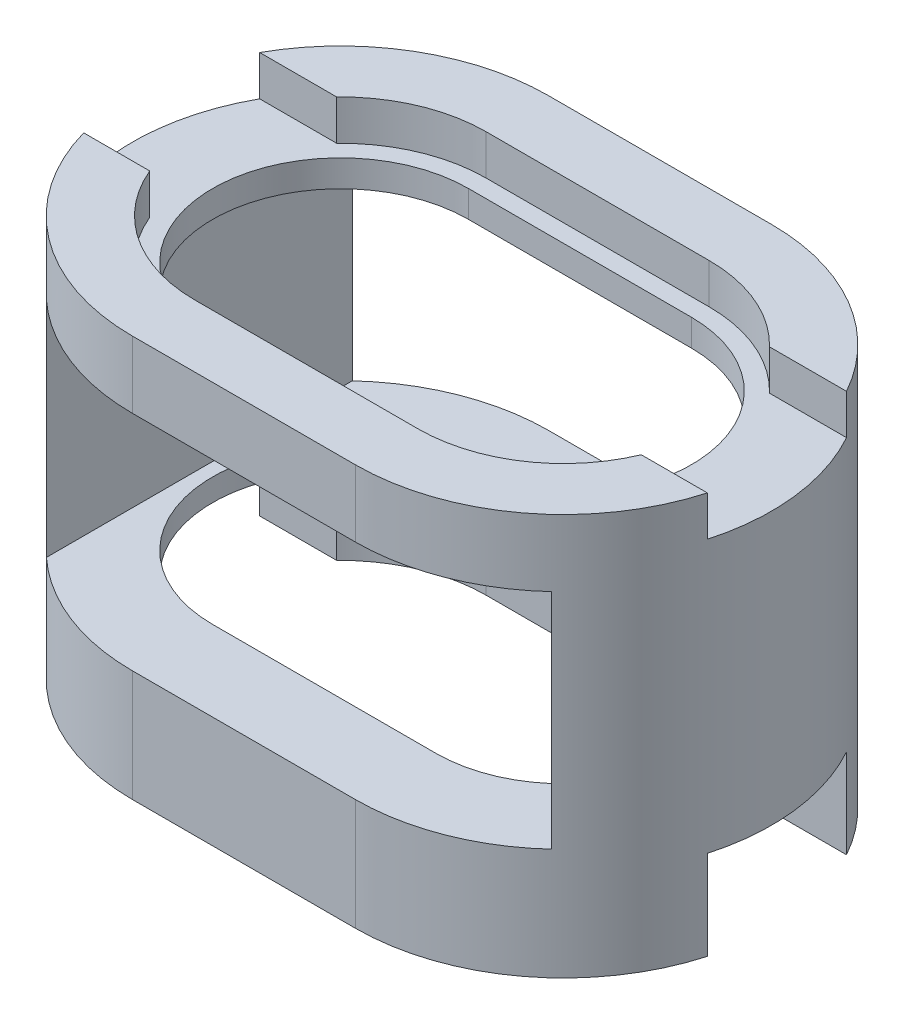
SolidWorks part; units mm, degrees
ref_plane "Front Plane" through (0, 0, 0) normal (0, 0, 1) x (1, 0, 0)
ref_plane "Top Plane" through (0, 0, 0) normal (0, 1, 0) x (1, 0, 0)
ref_plane "Right Plane" through (0, 0, 0) normal (1, 0, 0) x (0, 0, -1)
sketch "Sketch1" plane through (0, 0, 0) normal (0, 1, 0) x (1, 0, 0)
  line L0 (0, 0) -> (5, 0) construction
  line L1 (0, 3.2665) -> (5, 3.2665)
  line L2 (0, -3.2665) -> (5, -3.2665)
  line L3 (0, 4.6665) -> (5, 4.6665)
  line L4 (0, -4.6665) -> (5, -4.6665)
  arc A0 (0, 3.2665) -> (0, -3.2665) centre (0, 0) ccw
  arc A1 (5, -3.2665) -> (5, 3.2665) centre (5, 0) ccw
  arc A2 (5, -4.6665) -> (5, 4.6665) centre (5, 0) ccw
  arc A3 (0, 4.6665) -> (0, -4.6665) centre (0, 0) ccw
  point P3 (2.5, 0)
  point P8 (0, 0)
  point P15 (0, 0)
  point P16 (0, 0)
  dimension "D1" = 1.4
extrude "Boss-Extrude1" add sketch "Sketch1" along normal blind 9
ref_plane "Plane1" through (0, 2, 0) normal (0, 1, 0) x (1, 0, 0)
sketch "Sketch2" plane through (0, 2, 0) normal (0, 1, 0) x (1, 0, 0)
  line L0 (0, 0) -> (5, 0) construction
  line L1 (0, 2.8665) -> (5, 2.8665)
  line L2 (0, -2.8665) -> (5, -2.8665)
  line L3 (0, 3.2665) -> (5, 3.2665)
  line L4 (0, -3.2665) -> (5, -3.2665)
  arc A0 (0, 2.8665) -> (0, -2.8665) centre (0, 0) ccw
  arc A1 (5, -2.8665) -> (5, 2.8665) centre (5, 0) ccw
  arc A2 (5, -3.2665) -> (5, 3.2665) centre (5, 0) ccw
  arc A3 (0, 3.2665) -> (0, -3.2665) centre (0, 0) ccw
  point P3 (2.5, 0)
  point P14 (0, 0)
  point P15 (0, 0)
  point P16 (0, 0)
  dimension "D1" = 0.4
extrude "Boss-Extrude2" add sketch "Sketch2" along normal blind 6.1
sketch "Sketch3" plane through (0, 0, 4.6665) normal (0, 0, 1) x (1, 0, 0)
  line L1 (-3.165, 7.5) -> (8.165, 7.5)
  line L2 (-3.165, 7.5) -> (-3.165, 2.5)
  line L3 (-3.165, 2.5) -> (8.165, 2.5)
  line L4 (8.165, 7.5) -> (8.165, 2.5)
  line L5 (-3.165, 7.5) -> (8.165, 2.5) construction
  line L6 (-3.165, 2.5) -> (8.165, 7.5) construction
  point P0 (2.5, 5)
  dimension "D1" = 5
extrude "Cut-Extrude1" cut sketch "Sketch3" against normal blind 10
sketch "Sketch4" plane through (0, 9, 0) normal (0, 1, 0) x (1, 0, 0)
  line L0 (5, 3.2665) -> (0, 3.2665) construction
  line L1 (10, -1.2665) -> (-5, -1.2665)
  line L2 (10, -1.2665) -> (10, 2.2665)
  line L3 (10, 2.2665) -> (-5, 2.2665)
  line L4 (-5, -1.2665) -> (-5, 2.2665)
  line L5 (10, -1.2665) -> (-5, 2.2665) construction
  line L6 (10, 2.2665) -> (-5, -1.2665) construction
  line L7 (0, -3.2665) -> (5, -3.2665) construction
  point P0 (2.5, 0.5)
  point P9 (0, 0)
  point P10 (0, 0)
  point P11 (0, 0)
  dimension "D1" = 1
  dimension "D2" = 2
  dimension "D3" = 15
extrude "Cut-Extrude2" cut sketch "Sketch4" against normal blind 0.9
sketch "Sketch5" plane through (0, 0, 0) normal (0, -1, 0) x (1, 0, 0)
  line L2 (10, -2.2665) -> (-5, -2.2665)
  line L3 (10, -2.2665) -> (10, 1.2665)
  line L4 (10, 1.2665) -> (-5, 1.2665)
  line L5 (-5, -2.2665) -> (-5, 1.2665)
  line L6 (10, -2.2665) -> (-5, 1.2665) construction
  line L8 (10, 1.2665) -> (-5, -2.2665) construction
  point P0 (2.5, -0.5)
extrude "Cut-Extrude3" cut sketch "Sketch5" against normal blind 2
